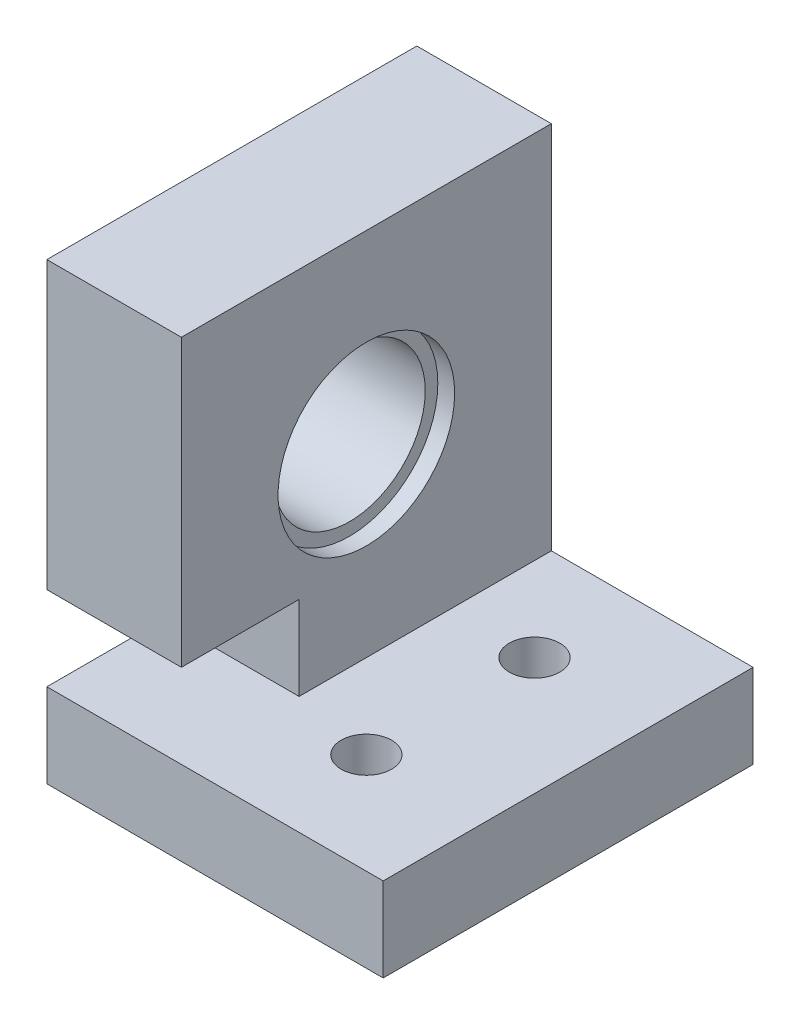
SolidWorks part; units mm, degrees
material "1060 合金"
ref_plane "前视基准面" through (0, 0, 0) normal (0, 0, 1) x (1, 0, 0)
ref_plane "上视基准面" through (0, 0, 0) normal (0, 1, 0) x (1, 0, 0)
ref_plane "右视基准面" through (0, 0, 0) normal (1, 0, 0) x (0, 0, -1)
sketch "草图1" plane through (0, 0, 0) normal (1, 0, 0) x (0, 0, -1)
  line L0 (0, 15) -> (0, 4) construction
  line L1 (-11, 15) -> (11, 15)
  line L2 (-11, 15) -> (-11, -15)
  line L3 (-11, -15) -> (11, -15)
  line L4 (11, 15) -> (11, -15)
  line L5 (-11, 15) -> (11, -15) construction
  line L6 (-11, -15) -> (11, 15) construction
  circle A0 centre (0, 4) radius 4.5
  circle A1 centre (0, 4) radius 5.25
  point P0 (0, 0)
  dimension "D4" = 9
  dimension "D5" = 10.5
  dimension "D1" = 30
  dimension "D2" = 22
  dimension "D3" = 11
extrude "凸台-拉伸1" add sketch "草图1" along normal blind 8 contours L2 L1 L4 L3
sketch "草图2" plane through (0, 0, 0) normal (-1, 0, 0) x (0, 0, 1)
  line L0 (0, 15) -> (0, 4) construction
  line L1 (11, 15) -> (-11, 15) construction
  circle A0 centre (0, 4) radius 4.5
  dimension "D2" = 9
  dimension "D1" = 11
extrude "切除-拉伸1" cut sketch "草图2" against normal through all
sketch "草图3" plane through (0, 0, 0) normal (-1, 0, 0) x (0, 0, 1)
  line L0 (11, -15) -> (11, -10) construction
  line L1 (11, 15) -> (11, -15) construction
  line L3 (11, -10) -> (4, -10)
  line L4 (11, -10) -> (11, -2)
  line L5 (11, -2) -> (4, -2)
  line L6 (4, -10) -> (4, -2)
  dimension "D1" = 5
  dimension "D2" = 7
  dimension "D3" = 8
extrude "切除-拉伸2" cut sketch "草图3" against normal through all
sketch "草图4" plane through (0, 0, 0) normal (-1, 0, 0) x (0, 0, 1)
  circle A0 centre (0, 4) radius 5.25
  dimension "D1" = 10.5
extrude "切除-拉伸3" cut sketch "草图4" against normal blind 1
sketch "草图5" plane through (8, 0, 0) normal (1, 0, 0) x (0, 0, -1)
  circle A0 centre (0, 4) radius 5.25
  dimension "D1" = 10.5
extrude "切除-拉伸4" cut sketch "草图5" against normal blind 1
sketch "草图6" plane through (8, 0, 0) normal (1, 0, 0) x (0, 0, -1)
  line L1 (-11, -10) -> (11, -10)
  line L2 (-11, -10) -> (-11, -15)
  line L3 (-11, -15) -> (11, -15)
  line L4 (11, -10) -> (11, -15)
extrude "凸台-拉伸2" add sketch "草图6" along normal blind 12
sketch "草图7" plane through (0, -15, 0) normal (0, -1, 0) x (1, 0, 0)
  line L0 (20, -11) -> (20, -5) construction
  line L1 (20, 11) -> (20, -11) construction
  line L2 (20, -5) -> (13, -5) construction
  line L10 (9.8, -5) -> (11.4, -7.7713)
  line L11 (11.4, -7.7713) -> (14.6, -7.7713)
  line L12 (14.6, -7.7713) -> (16.2, -5)
  line L13 (16.2, -5) -> (14.6, -2.2287)
  line L14 (14.6, -2.2287) -> (11.4, -2.2287)
  line L15 (11.4, -2.2287) -> (9.8, -5)
  circle A0 centre (13, -5) radius 2.7713 construction
  dimension "D1" = 6
  dimension "D2" = 7
  dimension "D3" = 3.2
  dimension "D4" = 3.8
extrude "切除-拉伸5" cut sketch "草图7" against normal blind 2.5
pattern_linear "阵列(线性)1" count 2 spacing 10 along (0, 0, 1) of "切除-拉伸5"
sketch "草图8" plane through (0, -12.5, 0) normal (0, -1, 0) x (1, 0, 0)
  line L0 (20, 11) -> (20, -11) construction
  line L1 (20, 11) -> (0, 11) construction
  circle A0 centre (13, 5) radius 1.5
  dimension "D1" = 7
  dimension "D2" = 3
  dimension "D3" = 6
extrude "切除-拉伸6" cut sketch "草图8" against normal through all
pattern_linear "阵列(线性)2" count 2 spacing 10 along (0, 0, -1) of "切除-拉伸6"
sketch "草图10" plane through (0, -10, 0) normal (0, 1, 0) x (1, 0, 0)
  line L0 (0, -4) -> (8, -4)
  line L1 (8, -4) -> (8, 11)
  line L2 (8, 11) -> (20, 11)
  line L3 (20, 11) -> (20, -11)
  line L4 (20, -11) -> (0, -11)
  line L5 (0, -11) -> (0, -4)
extrude "凸台-拉伸3" add sketch "草图10" along normal blind 3
sketch "草图12" plane through (0, -10, 0) normal (0, -1, 0) x (1, 0, 0)
  circle A0 centre (13, 5) radius 1.5
extrude "切除-拉伸7" cut sketch "草图12" against normal through all
sketch "草图14" plane through (0, -10, 0) normal (0, -1, 0) x (1, 0, 0)
  circle A0 centre (13, -5) radius 1.5
extrude "切除-拉伸8" cut sketch "草图14" against normal through all
sketch "草图15" plane through (0, -12.5, 0) normal (0, -1, 0) x (1, 0, 0)
  line L1 (16.2, 5) -> (14.6, 7.7713)
  line L2 (14.6, 7.7713) -> (11.4, 7.7713)
  line L3 (11.4, 7.7713) -> (9.8, 5)
  line L4 (9.8, 5) -> (11.4, 2.2287)
  line L5 (11.4, 2.2287) -> (14.6, 2.2287)
  line L6 (14.6, 2.2287) -> (16.2, 5)
  circle A0 centre (13, 5) radius 2.7713 construction
extrude "切除-拉伸9" cut sketch "草图15" against normal blind 3
pattern_linear "阵列(线性)3" count 2 spacing 10 along (0, 0, -1) of "切除-拉伸9"
sketch "草图16" plane through (0, -15, 0) normal (0, -1, 0) x (1, 0, 0)
  line L1 (20, 11) -> (0, 11)
  line L2 (20, 11) -> (20, -11)
  line L3 (20, -11) -> (0, -11)
  line L4 (0, 11) -> (0, -11)
extrude "切除-拉伸10" cut sketch "草图16" against normal blind 3
